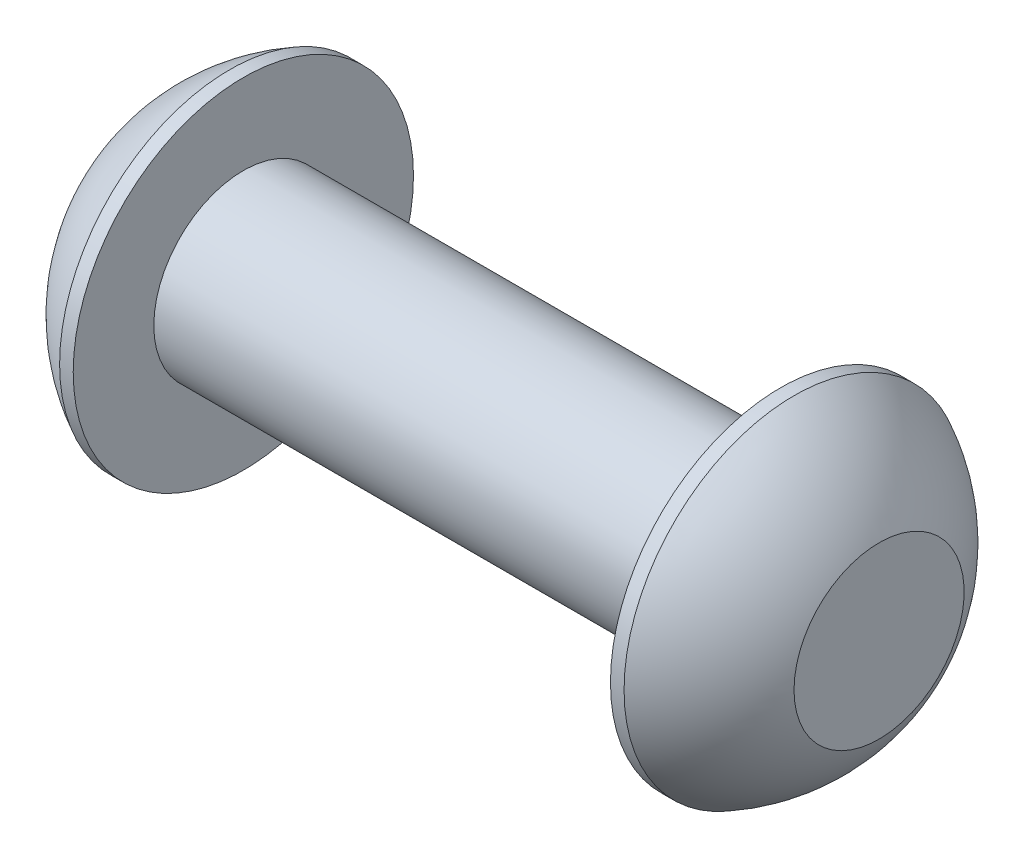
SolidWorks part; units mm, degrees
ref_plane "Front Plane" through (0, 0, 0) normal (0, 0, 1) x (1, 0, 0)
ref_plane "Top Plane" through (0, 0, 0) normal (0, 1, 0) x (1, 0, 0)
ref_plane "Right Plane" through (0, 0, 0) normal (1, 0, 0) x (0, 0, -1)
sketch "Sketch2" plane through (0, 0, 0) normal (0, 0, 1) x (1, 0, 0)
  line L0 (-1.1781, 0) -> (27.4341, 0) construction
  line L1 (17.75, 2.5) -> (2.75, 2.5)
  line L2 (2.75, 2.5) -> (2.75, 4.75)
  line L3 (2.75, 4.75) -> (2.37, 4.75)
  line L4 (0, 0) -> (20.5, 0) construction
  line L5 (2.75, -4.75) -> (2.37, -4.75) construction
  line L7 (20.5, 0) -> (0, 0)
  line L8 (0, 2.375) -> (0, -2.375) construction
  line L9 (0, 0) -> (0, 2.375)
  line L11 (18.195, -2.055) -> (17.75, -2.5) construction
  line L13 (2.75, 4.75) -> (2.75, 2.5) construction
  line L14 (17.75, 2.5) -> (17.75, 4.75)
  line L15 (17.75, 4.75) -> (18.13, 4.75)
  line L17 (20.5, 0) -> (20.5, 2.375)
  line L18 (17.75, 4.75) -> (18.13, 4.75)
  line L19 (17.75, 2.5) -> (17.75, 4.75)
  arc A0 (20.5, 2.375) -> (18.13, 4.75) centre (15.745, 0) ccw
  arc A1 (0, 2.375) -> (2.37, 4.75) centre (4.755, 0) cw
  dimension "D1" = 15
revolve "Revolve1" add sketch "Sketch2" angle 360 about L0
